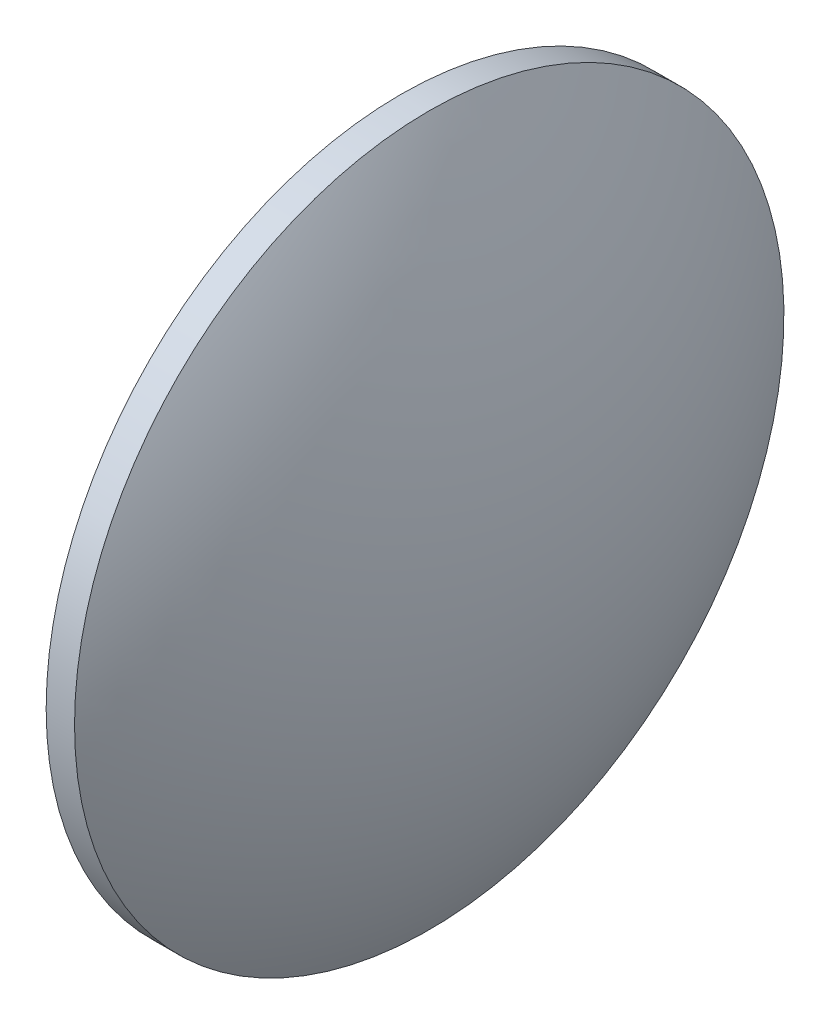
SolidWorks part; units mm, degrees
ref_plane "前视基准面" through (0, 0, 0) normal (0, 0, 1) x (1, 0, 0)
ref_plane "上视基准面" through (0, 0, 0) normal (0, 1, 0) x (1, 0, 0)
ref_plane "右视基准面" through (0, 0, 0) normal (1, 0, 0) x (0, 0, -1)
sketch "草图1" plane through (0, 0, 0) normal (0, 0, 1) x (1, 0, 0)
  line L0 (315.8819, 191.402) -> (364.6706, 191.402) construction
  line L1 (338.3866, 241.402) -> (342.3866, 241.402)
  line L2 (342.3866, 241.402) -> (342.3866, 141.402)
  line L3 (342.3866, 141.402) -> (338.3866, 141.402)
  line L4 (338.3866, 141.402) -> (338.3866, 241.402)
  arc A0 (338.3866, 241.402) -> (338.3866, 141.402) centre (422.3496, 191.402) ccw
  arc A1 (342.3866, 141.402) -> (342.3866, 241.402) centre (258.4236, 191.402) ccw
  dimension "D1" = 4
  dimension "D2" = 100
revolve "旋转1" add sketch "草图1" angle 360 about L0
